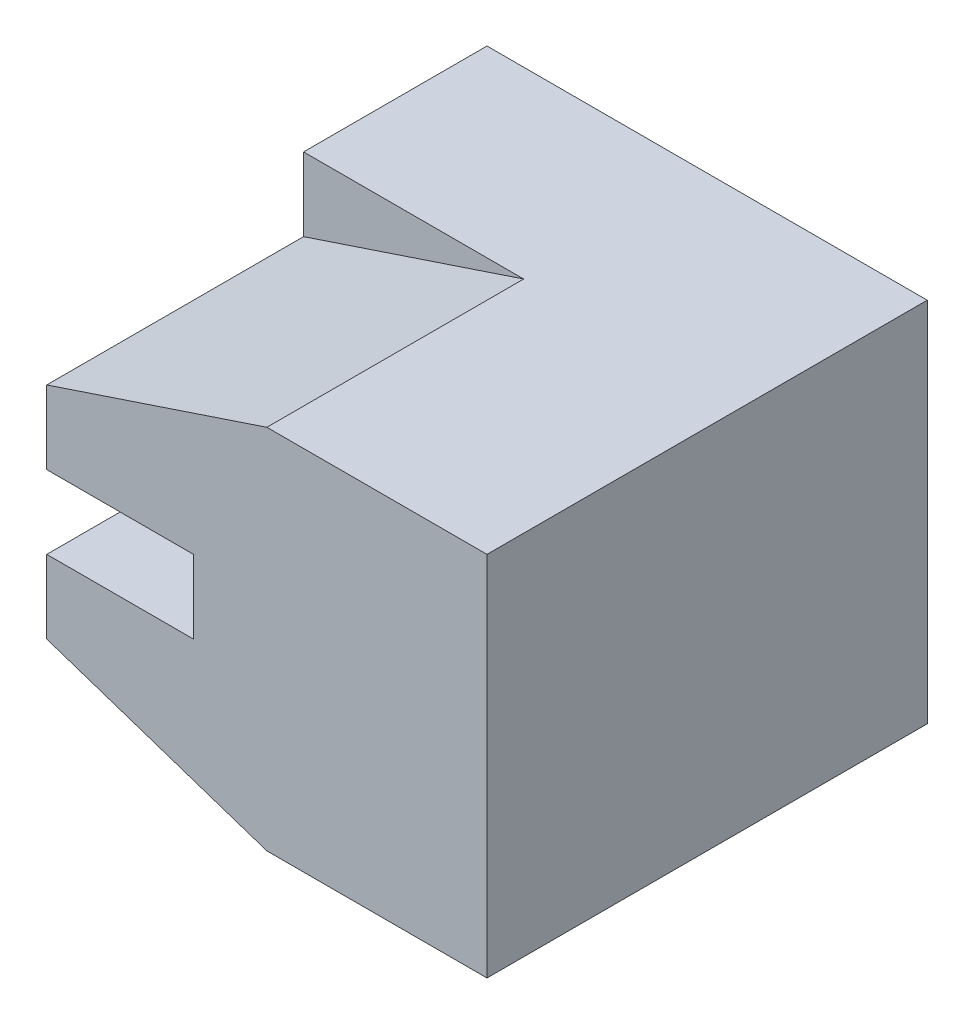
SolidWorks part; units mm, degrees
ref_plane "Front" through (0, 0, 0) normal (0, 0, 1) x (1, 0, 0)
ref_plane "Top" through (0, 0, 0) normal (0, 1, 0) x (1, 0, 0)
ref_plane "Right" through (0, 0, 0) normal (1, 0, 0) x (0, 0, -1)
sketch "Sketch1" plane through (0, 0, 0) normal (0, 1, 0) x (1, 0, 0)
  line L1 (-3, -3) -> (3, -3)
  line L2 (-3, -3) -> (-3, 3)
  line L3 (-3, 3) -> (3, 3)
  line L4 (3, -3) -> (3, 3)
  line L5 (-3, -3) -> (3, 3) construction
  line L6 (-3, 3) -> (3, -3) construction
  point P0 (0, 0)
  dimension "D1" = 6
  dimension "D2" = 6
extrude "Boss-Extrude1" add sketch "Sketch1" along normal blind 5
sketch "Sketch2" plane through (-3, 0, 0) normal (-1, 0, 0) x (0, 0, 1)
  line L0 (3, 5) -> (3, 0) construction
  line L3 (-0.5, 2) -> (6.5, 2)
  line L5 (-0.5, 2) -> (-0.5, 3)
  line L6 (-0.5, 3) -> (6.5, 3)
  line L7 (6.5, 2) -> (6.5, 3)
  line L8 (-0.5, 2) -> (6.5, 3) construction
  line L9 (-0.5, 3) -> (6.5, 2) construction
  point P0 (3, 2.5)
  line M2 (3, 0) -> (3, 5)
  dimension "D1" = 1
  dimension "D2" = 7
extrude "Cut-Extrude1" cut sketch "Sketch2" against normal blind 2 contours L6 L5 L3 M2
sketch "Sketch3" plane through (0, 0, 3) normal (0, 0, 1) x (1, 0, 0)
  line L0 (-3, 4) -> (0, 5)
  line L1 (0, 0) -> (-3, 1)
  line L8 (-3, 3) -> (-1, 3)
  line L9 (-1, 3) -> (-1, 2)
  line L10 (-1, 2) -> (-3, 2)
  line L11 (-3, 2) -> (-3, 0)
  line L12 (-3, 0) -> (3, 0)
  line L13 (3, 0) -> (3, 5)
  line L14 (3, 5) -> (-3, 5)
  line L15 (-3, 5) -> (-3, 3)
  line L16 (-3, 3) -> (-1, 3)
  line L17 (-1, 3) -> (-1, 2)
  line L18 (-1, 2) -> (-3, 2)
  line L19 (-3, 2) -> (-3, 0)
  line L20 (-3, 0) -> (3, 0)
  line L21 (3, 0) -> (3, 5)
  line L22 (3, 5) -> (-3, 5)
  line L23 (-3, 5) -> (-3, 3)
  line M12 (-3, 2) -> (-3, 0)
  line M13 (-3, 0) -> (3, 0)
  line M15 (3, 5) -> (-3, 5)
  line M16 (-3, 5) -> (-3, 3)
  dimension "D1" = 0
extrude "Cut-Extrude2" cut sketch "Sketch3" against normal blind 3.5 contours L0 M16 M15 | L1 M13 M12
